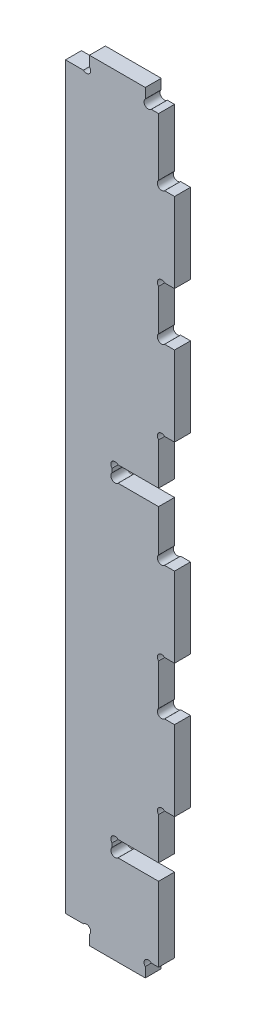
SolidWorks part; units mm, degrees
ref_plane "Plan de face" through (0, 0, 0) normal (0, 0, 1) x (1, 0, 0)
ref_plane "Plan de dessus" through (0, 0, 0) normal (0, 1, 0) x (1, 0, 0)
ref_plane "Plan de droite" through (0, 0, 0) normal (1, 0, 0) x (0, 0, -1)
sketch "Esquisse1" plane through (0, 0, 0) normal (0, 0, 1) x (1, 0, 0)
  line L0 (-10, 0) -> (51, 0) construction
  line L1 (0, -10) -> (0, 300) construction
  line L2 (41, 300) -> (41, -10) construction
  line L3 (-10, 290) -> (51, 290) construction
  line L4 (-23.4361, 159) -> (58.8143, 159) construction
  line L5 (58.8143, 37) -> (-23.4361, 37) construction
  line L6 (-23.4361, 6) -> (58.8143, 6) construction
  line L7 (0, 6) -> (6.7373, 6)
  line L9 (35, 300) -> (35, -10) construction
  line L10 (9, -5.4673) -> (9, 16.8453) construction
  line L11 (9, 6) -> (2.212, -0.788) construction
  line L12 (47.702, 98) -> (12.0839, 98) construction
  line L13 (45.7629, 88) -> (29.5366, 88) construction
  line L14 (45.7629, 58) -> (30.7239, 58) construction
  line L15 (43.9819, 73) -> (29.5366, 73) construction
  line L16 (14.371, 40) -> (36.4549, 40) construction
  line L17 (36.4549, 34) -> (14.371, 34) construction
  line L18 (17.5, 40) -> (26.9355, 30.5645) construction
  line L19 (9, 3.7373) -> (9, 0)
  line L20 (35, 58) -> (42.2338, 50.7662) construction
  line L21 (9, 0) -> (30, 0)
  line L22 (35, 40) -> (19.7627, 40)
  line L23 (17.5, 37.7373) -> (17.5, 36.2627)
  line L24 (19.7627, 34) -> (35, 34)
  line L25 (37.2627, 108) -> (41, 108)
  line L26 (37.2627, 88) -> (41, 88)
  line L27 (41, 108) -> (41, 138)
  line L28 (37.2627, 58) -> (41, 58)
  line L29 (41, 88) -> (41, 58)
  line L30 (37.2627, 138) -> (41, 138)
  line L31 (35, 156) -> (19.7627, 156)
  line L32 (19.7627, 162) -> (35, 162)
  line L33 (17.5, 158.2627) -> (17.5, 159.7373)
  line L34 (35, 105.7373) -> (35, 90.2627)
  line L35 (37.2627, 260) -> (41, 260)
  line L36 (41, 230) -> (41, 260)
  line L37 (37.2627, 230) -> (41, 230)
  line L38 (35, 212.2627) -> (35, 227.7373)
  line L39 (37.2627, 210) -> (41, 210)
  line L40 (41, 210) -> (41, 180)
  line L41 (37.2627, 180) -> (41, 180)
  line L42 (-6.1098, 145) -> (9, 145) construction
  line L43 (9, 290) -> (30, 290)
  line L44 (9, 286.2627) -> (9, 290)
  line L45 (0, 284) -> (6.7373, 284)
  line L46 (35, 55.7373) -> (35, 40)
  line L47 (35, 34) -> (35, 6)
  line L48 (35, 140.2627) -> (35, 156)
  line L49 (35, 162) -> (35, 177.7373)
  line L50 (35, 262.2627) -> (35, 284)
  line L51 (0, 284) -> (0, 6)
  line L52 (30, -6.1798) -> (30, 12.4703) construction
  line L53 (30, 6) -> (38.7957, -2.7957) construction
  line L54 (32.2627, 6) -> (35, 6)
  line L55 (30, 0) -> (30, 3.7373)
  line L56 (30, 290) -> (30, 286.2627)
  line L57 (32.2627, 284) -> (35, 284)
  arc A0 (9, 3.7373) -> (6.7373, 6) centre (7.8686, 4.8686) ccw
  arc A1 (19.7627, 40) -> (17.5, 37.7373) centre (18.6314, 38.8686) ccw
  arc A2 (19.7627, 34) -> (17.5, 36.2627) centre (18.6314, 35.1314) cw
  arc A3 (37.2627, 58) -> (35, 55.7373) centre (36.1314, 56.8686) ccw
  arc A4 (37.2627, 88) -> (35, 90.2627) centre (36.1314, 89.1314) cw
  arc A5 (37.2627, 108) -> (35, 105.7373) centre (36.1314, 106.8686) ccw
  arc A6 (37.2627, 138) -> (35, 140.2627) centre (36.1314, 139.1314) cw
  arc A7 (19.7627, 162) -> (17.5, 159.7373) centre (18.6314, 160.8686) ccw
  arc A8 (19.7627, 156) -> (17.5, 158.2627) centre (18.6314, 157.1314) cw
  arc A9 (37.2627, 260) -> (35, 262.2627) centre (36.1314, 261.1314) cw
  arc A10 (37.2627, 230) -> (35, 227.7373) centre (36.1314, 228.8686) ccw
  arc A11 (37.2627, 210) -> (35, 212.2627) centre (36.1314, 211.1314) cw
  arc A12 (37.2627, 180) -> (35, 177.7373) centre (36.1314, 178.8686) ccw
  arc A13 (9, 286.2627) -> (6.7373, 284) centre (7.8686, 285.1314) cw
  arc A14 (32.2627, 6) -> (30, 3.7373) centre (31.1314, 4.8686) ccw
  arc A15 (32.2627, 284) -> (30, 286.2627) centre (31.1314, 285.1314) cw
  dimension "D9" = 5
  dimension "D1" = 10
  dimension "D2" = 15
  dimension "D3" = 30
  dimension "D4" = 3
  dimension "D5" = 6
  dimension "D6" = 45
  dimension "D7" = 45
  dimension "D8" = 6
  dimension "D10" = 45
extrude "Extrusion1" add sketch "Esquisse1" along normal blind 6
sketch "Esquisse2" plane through (0, 0, 0) normal (0, 0, -1) x (-1, 0, 0)
  line L0 (0, 291.6343) -> (0, -14.6559) construction
  line L1 (-45.5647, 163) -> (16.457, 163) construction
  line L2 (-45.5647, 217) -> (16.457, 217) construction
  line L3 (-51.5848, 40) -> (20.8187, 40) construction
  line L4 (-8.9764, 218) -> (6.8637, 218) construction
  line L5 (-19.3074, 190) -> (11.682, 190) construction
  line L6 (-15, 204.1554) -> (-15, 187.7203) construction
  line L7 (-4, 171.3597) -> (-4, 154.8504) construction
  line L8 (3.7403, 167) -> (-10.9843, 167) construction
  line L9 (-30, 223.565) -> (-30, 159.9817) construction
  line L10 (-45.5647, 162) -> (16.457, 162) construction
  line L11 (-38.3306, 41) -> (20.8187, 41) construction
  line L12 (6.8637, 45) -> (-8.9764, 45) construction
  line L13 (-4, 34.1101) -> (-4, 50.7273) construction
  line L14 (9.6397, 68) -> (-28.2463, 68) construction
  line L15 (-15, 82.1813) -> (-15, 62.5967) construction
  line L17 (2.2233, 96) -> (-5.294, 96) construction
  circle A0 centre (-4, 167) radius 1.1
  circle A1 centre (-26, 167) radius 1.1
  circle A2 centre (-26, 213) radius 1.1
  circle A3 centre (-4, 213) radius 1.1
  circle A4 centre (-26, 223) radius 1.1
  circle A5 centre (-4, 223) radius 1.1
  circle A6 centre (-26, 269) radius 1.1
  circle A7 centre (-4, 269) radius 1.1
  circle A8 centre (-4, 45) radius 1.1
  circle A9 centre (-26, 45) radius 1.1
  circle A10 centre (-26, 91) radius 1.1
  circle A11 centre (-4, 91) radius 1.1
  circle A12 centre (-26, 101) radius 1.1
  circle A13 centre (-4, 101) radius 1.1
  circle A14 centre (-26, 147) radius 1.1
  circle A15 centre (-4, 147) radius 1.1
  dimension "D8" = 1
  dimension "D1" = 1
  dimension "D2" = 4
  dimension "D3" = 4
  dimension "D4" = 27
  dimension "D5" = 54
  dimension "D6" = 30
  dimension "D7" = 15
  dimension "D9" = 1
  dimension "D10" = 4
  dimension "D11" = 4
  dimension "D12" = 15
  dimension "D13" = 27
  dimension "D14" = 55
extrude "Enlèv. mat.-Extru.1" cut sketch "Esquisse2" against normal blind 2
